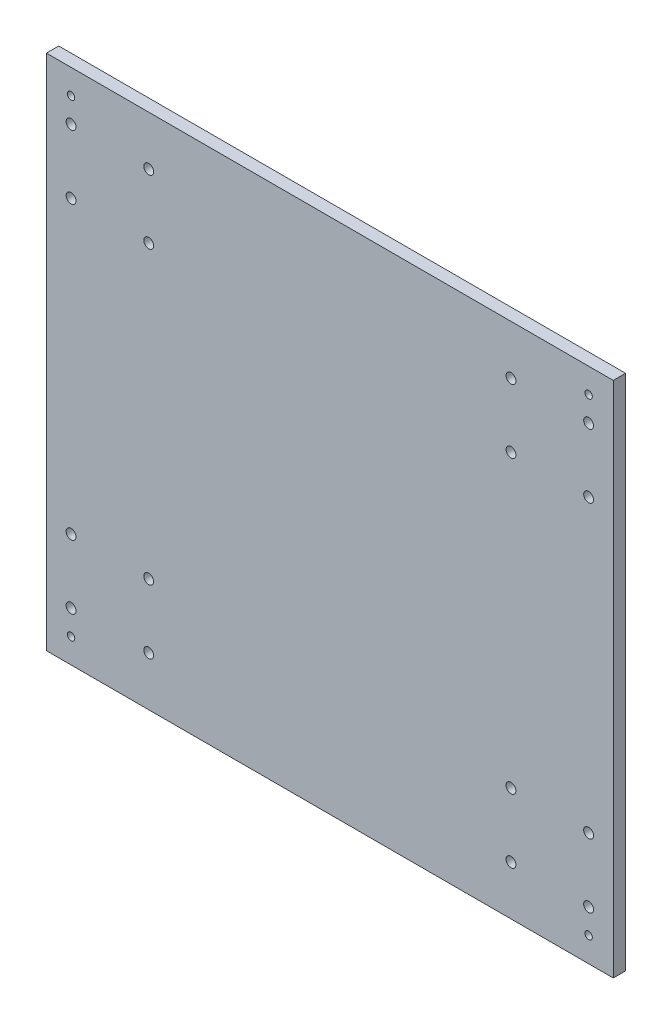
SolidWorks part; units mm, degrees
ref_plane "Ön Düzlem" through (0, 0, 0) normal (0, 0, 1) x (1, 0, 0)
ref_plane "Üst Düzlem" through (0, 0, 0) normal (0, 1, 0) x (1, 0, 0)
ref_plane "Sağ Düzlem" through (0, 0, 0) normal (1, 0, 0) x (0, 0, -1)
sketch "Çizim1" plane through (0, 0, 0) normal (0, 0, 1) x (1, 0, 0)
  line L0 (0, 105) -> (0, -105) construction
  line L1 (-115, -105) -> (115, -105)
  line L2 (-115, -105) -> (-115, 105)
  line L3 (-115, 105) -> (115, 105)
  line L4 (115, -105) -> (115, 105)
  line L5 (-115, -105) -> (115, 105) construction
  line L6 (-115, 105) -> (115, -105) construction
  line L7 (-115, 0) -> (115, 0) construction
  circle A0 centre (-105, 85) radius 2
  circle A1 centre (-73.5, 85) radius 2
  circle A2 centre (-105, 59) radius 2
  circle A3 centre (-73.5, 59) radius 2
  circle A4 centre (-105, 95) radius 1.5
  circle A5 centre (-105, -59) radius 2
  circle A6 centre (-105, -85) radius 2
  circle A7 centre (-105, -95) radius 1.5
  circle A8 centre (-73.5, -59) radius 2
  circle A9 centre (-73.5, -85) radius 2
  circle A10 centre (73.5, -85) radius 2
  circle A11 centre (73.5, -59) radius 2
  circle A12 centre (105, -95) radius 1.5
  circle A13 centre (105, -85) radius 2
  circle A14 centre (105, -59) radius 2
  circle A15 centre (105, 95) radius 1.5
  circle A16 centre (73.5, 59) radius 2
  circle A17 centre (105, 59) radius 2
  circle A18 centre (73.5, 85) radius 2
  circle A19 centre (105, 85) radius 2
  point P0 (0, 0)
  dimension "D5" = 3
  dimension "D6" = 4
  dimension "D8" = 31.5
  dimension "D1" = 210
  dimension "D2" = 230
  dimension "D3" = 10
  dimension "D4" = 10
  dimension "D7" = 26
  dimension "D9" = 10
  dimension "D10" = 20
extrude "Yükseklik-Ekstrüzyon1" add sketch "Çizim1" along normal blind 5
